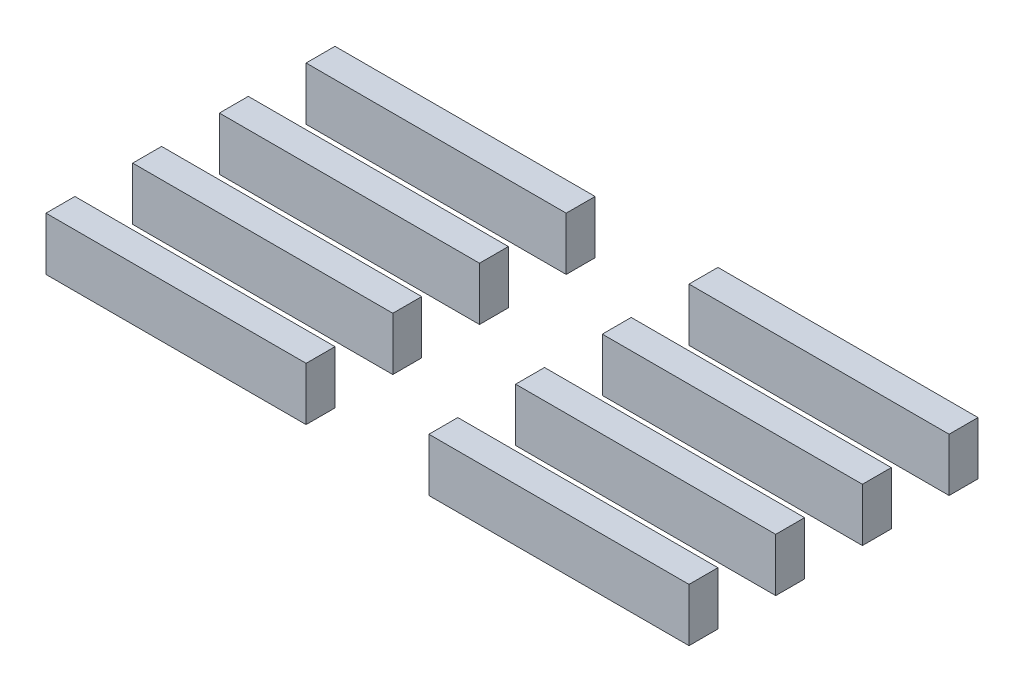
SolidWorks part; units mm, degrees
ref_plane "Front Plane" through (0, 0, 0) normal (0, 0, 1) x (1, 0, 0)
ref_plane "Top Plane" through (0, 0, 0) normal (0, 1, 0) x (1, 0, 0)
ref_plane "Right Plane" through (0, 0, 0) normal (1, 0, 0) x (0, 0, -1)
sketch "Sketch1" plane through (0, 0, 0) normal (0, 1, 0) x (1, 0, 0)
  line L0 (6.5, 18.5) -> (42.5, 18.5)
  line L1 (0, 0) -> (102, 0) construction
  line L2 (0, 0) -> (0, 53) construction
  line L3 (0, 53) -> (102, 53) construction
  line L4 (102, 0) -> (102, 53) construction
  line L5 (6.5, 6.5) -> (42.5, 6.5)
  line L6 (6.5, 6.5) -> (6.5, 10.5)
  line L7 (6.5, 10.5) -> (42.5, 10.5)
  line L8 (42.5, 6.5) -> (42.5, 10.5)
  line L9 (6.5, 22.5) -> (42.5, 22.5)
  line L10 (42.5, 18.5) -> (42.5, 22.5)
  line L11 (6.5, 18.5) -> (6.5, 22.5)
  line L12 (6.5, 30.5) -> (42.5, 30.5)
  line L13 (6.5, 34.5) -> (42.5, 34.5)
  line L14 (42.5, 30.5) -> (42.5, 34.5)
  line L15 (6.5, 30.5) -> (6.5, 34.5)
  line L16 (6.5, 42.5) -> (42.5, 42.5)
  line L17 (6.5, 46.5) -> (42.5, 46.5)
  line L18 (42.5, 42.5) -> (42.5, 46.5)
  line L19 (6.5, 42.5) -> (6.5, 46.5)
  line L20 (59.5, 6.5) -> (95.5, 6.5)
  line L21 (59.5, 10.5) -> (95.5, 10.5)
  line L22 (95.5, 6.5) -> (95.5, 10.5)
  line L23 (59.5, 6.5) -> (59.5, 10.5)
  line L24 (59.5, 18.5) -> (95.5, 18.5)
  line L25 (59.5, 22.5) -> (95.5, 22.5)
  line L26 (95.5, 18.5) -> (95.5, 22.5)
  line L27 (59.5, 18.5) -> (59.5, 22.5)
  line L28 (59.5, 30.5) -> (95.5, 30.5)
  line L29 (59.5, 34.5) -> (95.5, 34.5)
  line L30 (95.5, 30.5) -> (95.5, 34.5)
  line L31 (59.5, 30.5) -> (59.5, 34.5)
  line L32 (59.5, 42.5) -> (95.5, 42.5)
  line L33 (59.5, 46.5) -> (95.5, 46.5)
  line L34 (95.5, 42.5) -> (95.5, 46.5)
  line L35 (59.5, 42.5) -> (59.5, 46.5)
  dimension "D1" = 4
  dimension "D2" = 2
extrude "Boss-Extrude1" add sketch "Sketch1" along normal blind 7.35
